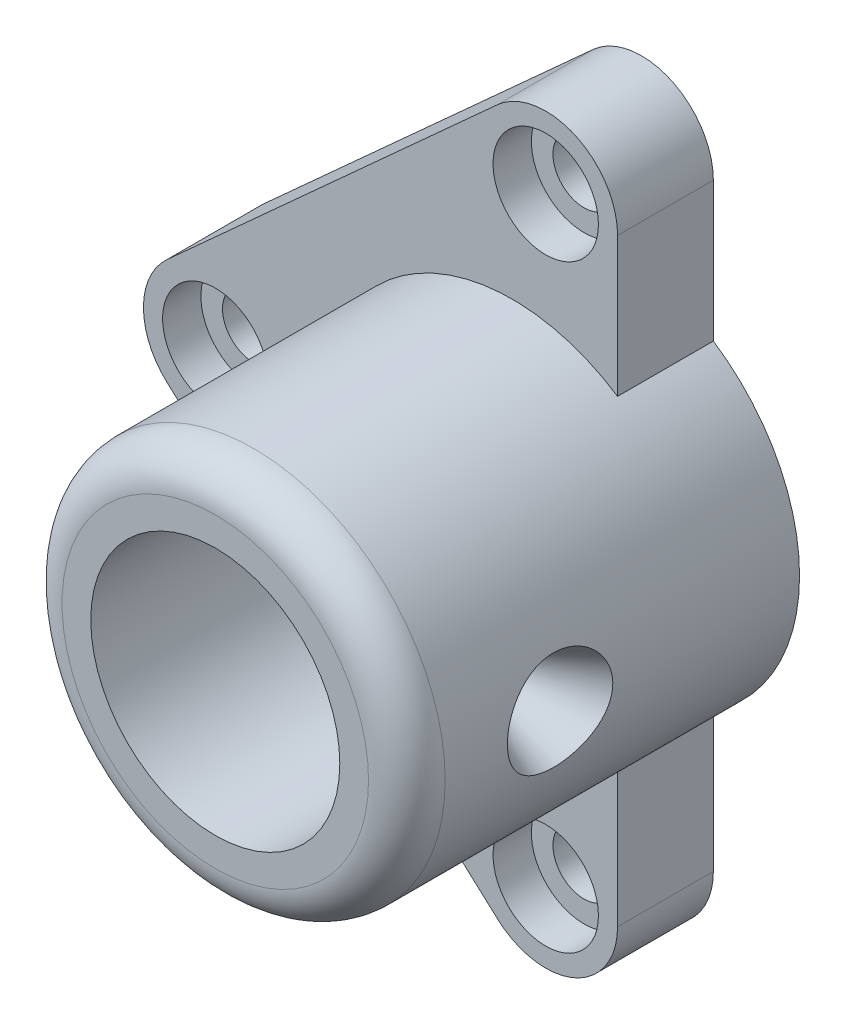
SolidWorks part; units mm, degrees
material "Plain Carbon Steel"
ref_plane "Front Plane" through (0, 0, 0) normal (1, 0, 0) x (0, 1, 0)
ref_plane "Top Plane" through (0, 0, 0) normal (0, 0, 1) x (0, 1, 0)
ref_plane "Right Plane" through (0, 0, 0) normal (0, 1, 0) x (-1, 0, 0)
sketch "Sketch1" plane through (0, 0, 0) normal (0, 0, 1) x (0, 1, 0)
  circle A0 centre (0, 0) radius 40
  circle A1 centre (0, 0) radius 26
  dimension "D1" = 80
  dimension "D2" = 52
extrude "Boss-Extrude1" add sketch "Sketch1" along normal blind 82 contours A0 | A1
sketch "Sketch2" plane through (0, 0, 0) normal (0, 0, 1) x (0, 1, 0)
  line L0 (-73.6173, 3.07) -> (-11.1173, 72.07)
  line L1 (11.1173, 72.07) -> (73.6173, 3.07)
  line L2 (62.5, -22) -> (33.4066, -22)
  line L3 (-62.5, -22) -> (-33.4066, -22)
  arc A1 (73.6173, 3.07) -> (62.5, -22) centre (62.5, -7) cw
  arc A2 (-11.1173, 72.07) -> (11.1173, 72.07) centre (0, 62) cw
  arc A3 (-73.6173, 3.07) -> (-62.5, -22) centre (-62.5, -7) ccw
  circle A4 centre (0, 62) radius 8.3856 construction
  circle A5 centre (62.5, -7) radius 8.4045 construction
  circle A6 centre (-62.5, -7) radius 10.0102 construction
  circle A7 centre (0, 0) radius 40 construction
  circle A8 centre (0, 0) radius 40
  arc A9 (-33.4066, -22) -> (33.4066, -22) centre (0, 0) ccw
  point P5 (-39.9505, -1.9901)
  point P6 (-39.9651, -1.67)
  point P17 (0, 0)
  point P18 (12.0767, 92.3856)
  point P19 (39.361, -39.1718)
  point P21 (39.7452, -4.5078)
  point P22 (39.9685, 1.588)
  point P25 (-36.3713, -16.6471)
  point P26 (-39.9159, -2.593)
  point P29 (39.984, 1.1317)
  point P30 (39.9159, -2.5925)
  dimension "D1" = 15
  dimension "D2" = 69
  dimension "D3" = 125
  dimension "D4" = 62.5
  dimension "D6" = 22
  dimension "D5" = 0
extrude "Boss-Extrude2" add sketch "Sketch2" along normal blind 20
sketch "Sketch4" plane through (0, 0, 20) normal (0, 0, 1) x (1, 0, 0)
  circle A0 centre (0, 0) radius 26
  dimension "D1" = 52
extrude "Cut-Extrude1" cut sketch "Sketch4" against normal blind 22
sketch "Sketch6" plane through (0, 0, 20) normal (0, 0, 1) x (1, 0, 0)
  circle A0 centre (-62, 0) radius 8.6613
  circle A1 centre (7, 62.5) radius 9.1727
  circle A2 centre (7, -62.5) radius 8.3329
  arc A3 (-3.07, -73.6173) -> (22, -62.5) centre (7, -62.5) ccw construction
  arc A4 (-72.07, 11.1173) -> (-72.07, -11.1173) centre (-62, 0) ccw construction
  arc A5 (22, 62.5) -> (-3.07, 73.6173) centre (7, 62.5) ccw construction
hole_wizard "CBORE for M10 Hex Head Bolt2" positions "3DSketch2" profile "Sketch8" counterbore size "M10" standard "ANSI Metric" end condition through all
sketch3d "3DSketch2"
  point P0 (-62, 0, 20)
  point P3 (7, 62.5, 20)
  point P6 (7, -62.5, 20)
sketch "Sketch8" plane through (-62, 0, 20) normal (1, 0, 0) x (0, -1, 0)
  line L0 (0, 0) -> (0, 20)
  line L1 (0, 20) -> (6.5, 20)
  line L3 (6.5, 20) -> (6.5, 8)
  line L4 (6.5, 8) -> (11, 8)
  line L5 (11, 8) -> (11, 0)
  line L7 (11, 0) -> (0, 0)
  line L11 (0, -6.35) -> (0, 107.95) construction
  dimension "Thru Hole Dia." = 13
  dimension "Thru Hole Depth" = 20
  dimension "C'Bore Dia." = 22
  dimension "C'Bore Depth" = 8
fillet "Fillet1" radius 8 1 edges at (40, 0, 82)
ref_plane "Plane1" through (40, 0, 0) normal (1, 0, 0) x (0, 1, 0)
sketch "Sketch20" plane through (40, 0, 0) normal (1, 0, 0) x (0, 1, 0)
  line L0 (0, 0) -> (0, 50) construction
  line L1 (-33.4066, 0) -> (33.4066, 0) construction
  point P1 (0, 50)
  dimension "D1" = 50
hole_wizard "CSK for M10 Flat Head Machine Screw12" positions "Sketch20" profile "Sketch21" countersink size "M10" standard "ANSI Metric"
sketch "Sketch21" plane through (40, 0, 50) normal (0, 1, 0) x (0, 0, -1)
  line L0 (0, 0) -> (0, 33.0043)
  line L1 (0, 33.0043) -> (5, 30)
  line L2 (5, 30) -> (5, 12.867)
  line L3 (5, 12.867) -> (11, 0)
  line L5 (11, 0) -> (0, 0)
  line L6 (-5, 12.867) -> (-11, 0) construction
  line L10 (0, 33.0043) -> (-5, 30) construction
  line L11 (0, -6.35) -> (0, 107.95) construction
  dimension "Hole Dia." = 10
  dimension "Hole Depth" = 30
  dimension "Near C'Sink Dia." = 22
  dimension "Near C'Sink Angle" = 50
  dimension "Drill Angle" = 118
sketch "Sketch22" plane through (0, 0, 0) normal (0, 0, -1) x (1, 0, 0)
  circle A0 centre (0, 0) radius 30
  dimension "D1" = 60
extrude "Cut-Extrude2" cut sketch "Sketch22" against normal blind 6
